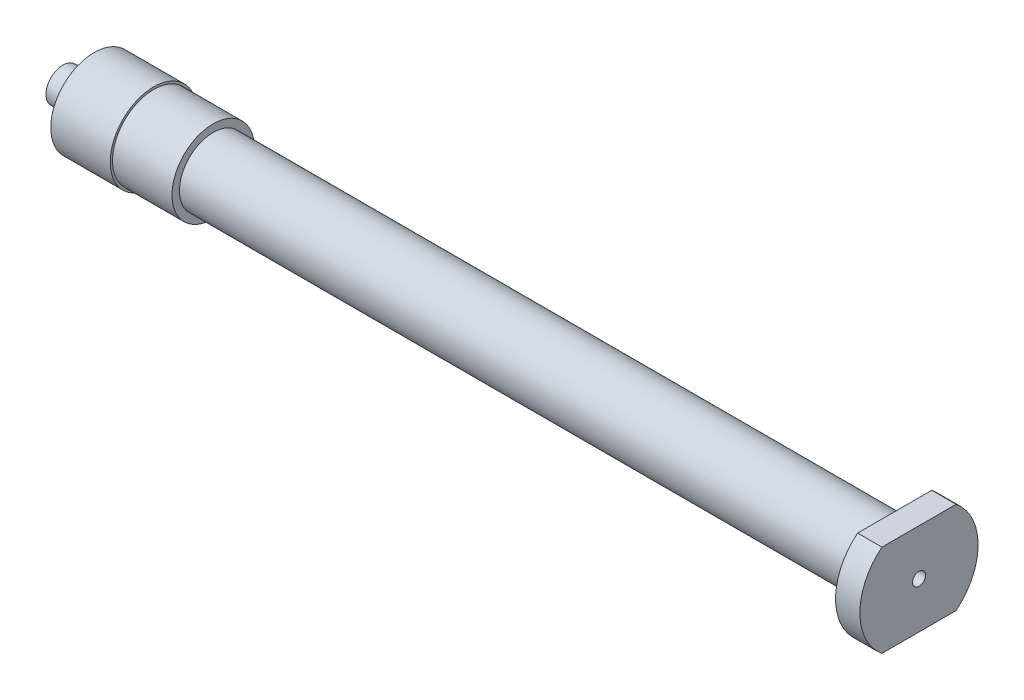
SolidWorks part; units mm, degrees
material "Silicon"
ref_plane "Front Plane" through (0, 0, 0) normal (0, 0, 1) x (1, 0, 0)
ref_plane "Top Plane" through (0, 0, 0) normal (0, 1, 0) x (1, 0, 0)
ref_plane "Right Plane" through (0, 0, 0) normal (1, 0, 0) x (0, 0, -1)
sketch "Sketch1" plane through (0, 0, 0) normal (0, 1, 0) x (1, 0, 0)
  line L0 (132.5479, 151.4753) -> (607.4548, -145.2795) construction
  line L1 (-49.285, 3.885) -> (49.285, 3.885) construction
  line L2 (-49.285, 3.885) -> (-49.285, -3.885) construction
  line L3 (-49.285, -3.885) -> (49.285, -3.885) construction
  line L4 (49.285, 3.885) -> (49.285, -3.885) construction
  line L5 (-49.285, 3.885) -> (49.285, -3.885) construction
  line L6 (-49.285, -3.885) -> (49.285, 3.885) construction
  line L7 (49.285, 0) -> (-49.285, 0) construction
  line L8 (-38.835, 5) -> (-38.835, -5) construction
  line L9 (-45.685, 5) -> (-31.985, 5) construction
  line L10 (-45.685, 5) -> (-45.685, -5) construction
  line L11 (-45.685, -5) -> (-31.985, -5) construction
  line L12 (-31.985, 5) -> (-31.985, -5) construction
  line L13 (46.485, 6.805) -> (49.285, 6.805) construction
  line L14 (46.485, 6.805) -> (46.485, -6.805) construction
  line L15 (46.485, -6.805) -> (49.285, -6.805) construction
  line L16 (49.285, 6.805) -> (49.285, -6.805) construction
  line L17 (-45.685, 0) -> (-31.985, 0) construction
  line L18 (46.485, 0) -> (49.285, 0) construction
  line L19 (-45.685, 4.74) -> (-31.985, 4.74) construction
  line L20 (-49.285, 1.95) -> (-61.5766, 1.95) construction
  line L21 (-49.285, 1.95) -> (-42.185, 2.3221) construction
  line L22 (49.285, 0.75) -> (-49.285, 0.75) construction
  line L23 (-49.285, 0.6) -> (-31.985, 0.6) construction
  line L24 (-49.285, 0.6) -> (-49.285, 1.95)
  line L25 (-49.285, 1.95) -> (-42.185, 2.3221)
  line L26 (-42.185, 2.3221) -> (-42.185, 4.1)
  line L27 (-42.185, 4.1) -> (-45.685, 4.1)
  line L28 (-45.685, 4.1) -> (-45.685, 5)
  line L29 (-45.685, 5) -> (-38.835, 5)
  line L30 (-38.835, 4.74) -> (-38.835, 5)
  line L31 (-38.835, 4.74) -> (-31.985, 4.74)
  line L32 (-31.985, 4.74) -> (-31.985, 3.885)
  line L33 (-31.985, 3.885) -> (46.485, 3.885)
  line L34 (-49.285, 0.6) -> (-31.985, 0.6)
  line L35 (-31.985, 0.6) -> (-31.985, 0.75)
  line L36 (-31.985, 0.75) -> (49.285, 0.75)
  line L37 (46.485, 3.885) -> (46.485, 6.805)
  line L38 (46.485, 6.805) -> (49.285, 6.805)
  line L39 (49.285, 6.805) -> (49.285, 0.75)
  point P0 (0, 0)
  dimension "D1" = 98.57
  dimension "D2" = 7.77
  dimension "D3" = 10
  dimension "D4" = 13.7
  dimension "D5" = 0.26
  dimension "D6" = 3.6
  dimension "D7" = 1.95
  dimension "D8" = 3
  dimension "D10" = 0.6
  dimension "D11" = 0.9
  dimension "D12" = 3.5
  dimension "D13" = 2.8
  dimension "D14" = 13.61
  dimension "D9" = 0.75
revolve "Revolve1" add sketch "Sketch1" angle 360 about L7
sketch "Sketch2" plane through (49.285, 0, 0) normal (1, 0, 0) x (0, 0, -1)
  line L0 (-9.5, -7.3) -> (9.5, -7.3)
  line L1 (-7.5, 5.3) -> (7.5, 5.3)
  line L2 (-7.5, 5.3) -> (-7.5, -5.3)
  line L3 (-7.5, -5.3) -> (7.5, -5.3)
  line L4 (7.5, 5.3) -> (7.5, -5.3)
  line L5 (-7.5, 5.3) -> (7.5, -5.3) construction
  line L6 (-7.5, -5.3) -> (7.5, 5.3) construction
  line L7 (9.5, 7.3) -> (9.5, -7.3)
  line L8 (-9.5, 7.3) -> (9.5, 7.3)
  line L9 (-9.5, 7.3) -> (-9.5, -7.3)
  point P0 (0, 0)
  dimension "D1" = 10.6
  dimension "D2" = 2
  dimension "D3" = 15
extrude "Cut-Extrude1" cut sketch "Sketch2" against normal up to surface (2.8 mm away) up to face at (46.485, 0, -3.885)
